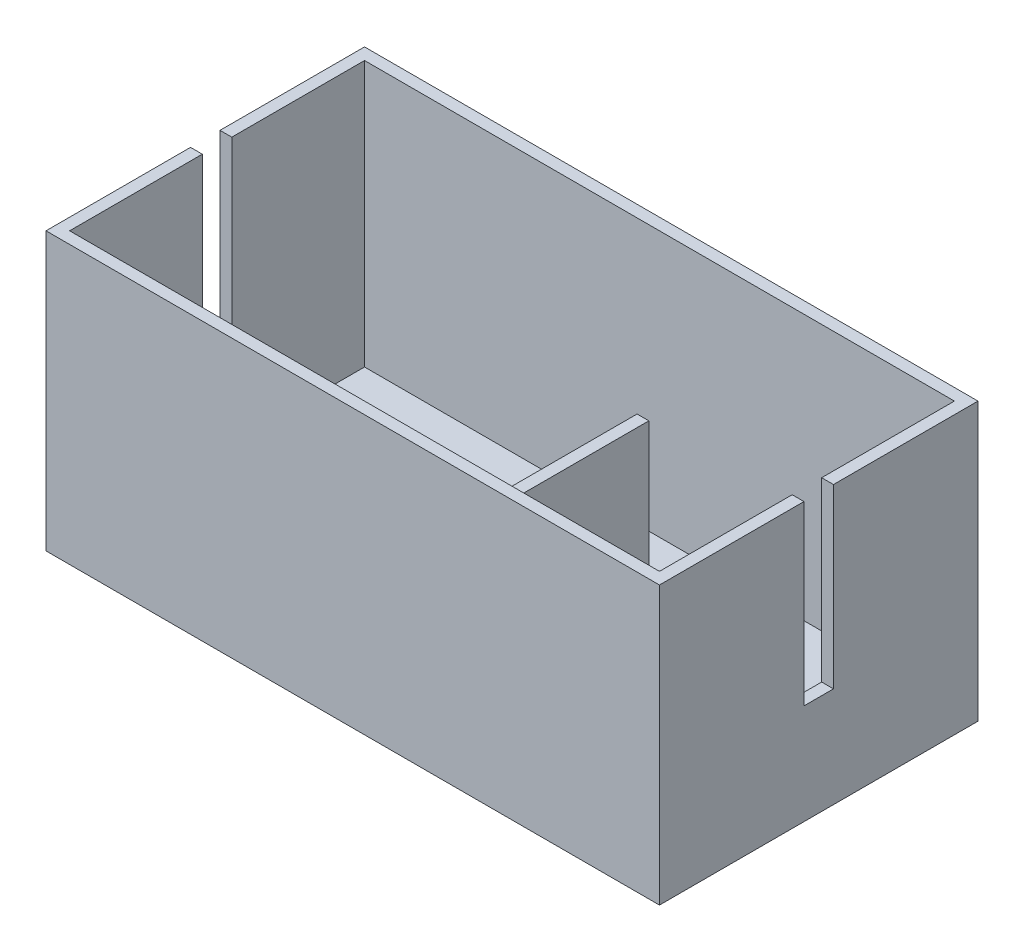
SolidWorks part; units mm, degrees
ref_plane "Front Plane" through (0, 0, 0) normal (0, 0, 1) x (1, 0, 0)
ref_plane "Top Plane" through (0, 0, 0) normal (0, 1, 0) x (1, 0, 0)
ref_plane "Right Plane" through (0, 0, 0) normal (1, 0, 0) x (0, 0, -1)
sketch "Sketch1" plane through (0, 0, 0) normal (0, 1, 0) x (1, 0, 0)
  line L1 (-50, 25) -> (50, 25)
  line L2 (-50, 25) -> (-50, -25)
  line L3 (-50, -25) -> (50, -25)
  line L4 (50, 25) -> (50, -25)
  line L5 (-50, 25) -> (50, -25) construction
  line L6 (-50, -25) -> (50, 25) construction
  line L7 (-52, 27) -> (52, 27)
  line L8 (-52, 27) -> (-52, -27)
  line L9 (-52, -27) -> (52, -27)
  line L10 (52, 27) -> (52, -27)
  line L11 (-52, 27) -> (52, -27) construction
  line L12 (-52, -27) -> (52, 27) construction
  point P0 (0, 0)
  point P6 (0, 0)
  dimension "D1" = 50
  dimension "D2" = 100
  dimension "D3" = 54
  dimension "D4" = 104
extrude "Boss-Extrude1" add sketch "Sketch1" along normal blind 45
sketch "Sketch2" plane through (0, 0, 0) normal (0, 1, 0) x (1, 0, 0)
  line L1 (-52, -27) -> (52, -27)
  line L2 (-52, -27) -> (-52, 27)
  line L3 (-52, 27) -> (52, 27)
  line L4 (52, -27) -> (52, 27)
  line L5 (-52, -27) -> (52, 27) construction
  line L6 (-52, 27) -> (52, -27) construction
  point P0 (0, 0)
extrude "Boss-Extrude2" add sketch "Sketch2" against normal blind 2
ref_plane "Plane1" through (0, 45, 0) normal (0, 1, 0) x (1, 0, 0)
sketch "Sketch3" plane through (0, 45, 0) normal (0, 1, 0) x (1, 0, 0)
  line L1 (52, -2.5) -> (50, -2.5)
  line L2 (52, -2.5) -> (52, 2.5)
  line L3 (52, 2.5) -> (50, 2.5)
  line L4 (50, -2.5) -> (50, 2.5)
  line L5 (52, -2.5) -> (50, 2.5) construction
  line L6 (52, 2.5) -> (50, -2.5) construction
  line L7 (-50, -2.5) -> (-52, -2.5)
  line L8 (-50, -2.5) -> (-50, 2.5)
  line L9 (-50, 2.5) -> (-52, 2.5)
  line L10 (-52, -2.5) -> (-52, 2.5)
  line L11 (-50, -2.5) -> (-52, 2.5) construction
  line L12 (-50, 2.5) -> (-52, -2.5) construction
  point P0 (51, 0)
  point P5 (-51, 0)
  point P10 (0, 0)
  point P11 (0, 0)
  point P14 (0, 0)
  point P17 (-24.7359, 8.177)
  dimension "D1" = 50
  dimension "D2" = 50
  dimension "D3" = 2
  dimension "D4" = 5
extrude "Cut-Extrude1" cut sketch "Sketch3" against normal blind 30
sketch "Sketch4" plane through (0, 0, 0) normal (0, 1, 0) x (1, 0, 0)
  line L0 (-50, -25) -> (50, -25) construction
  line L1 (20, -25) -> (22, -25)
  line L2 (20, -25) -> (20, 1.2012)
  line L3 (20, 1.2012) -> (22, 1.2012)
  line L4 (22, -25) -> (22, 1.2012)
  dimension "D1" = 30
  dimension "D2" = 2
extrude "Boss-Extrude3" add sketch "Sketch4" along normal blind 40
